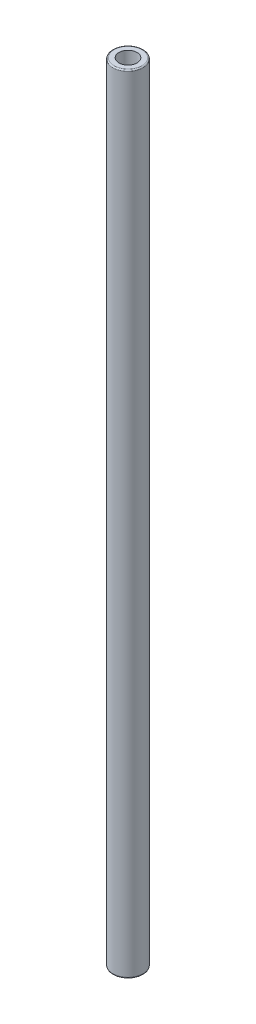
SolidWorks part; units mm, degrees
material "Thornel Mat VMA"
ref_plane "Front Plane" through (0, 0, 0) normal (0, 0, 1) x (1, 0, 0)
ref_plane "Top Plane" through (0, 0, 0) normal (0, 1, 0) x (1, 0, 0)
ref_plane "Right Plane" through (0, 0, 0) normal (1, 0, 0) x (0, 0, -1)
ref_plane "Front Plane-SSP" through (0, 0, 0) normal (0, 0, 1) x (1, 0, 0)
ref_plane "Top Plane-SSP" through (0, 0, 0) normal (0, 1, 0) x (1, 0, 0)
ref_plane "Right Plane-SSP" through (0, 0, 0) normal (1, 0, 0) x (0, 0, -1)
sketch "BagSide-SSP" plane through (0, 0, 0) normal (0, 0, 1) x (1, 0, 0)
  line L0 (0, 430) -> (0, 0)
  line L1 (0, 0) -> (179.1899, -17.0582)
  line L2 (179.1899, -17.0582) -> (130.767, 380)
  line L3 (130.767, 380) -> (0, 430)
  line L4 (130.767, 380) -> (0, 380)
  dimension "D1" = 430
  dimension "D2" = 140
  dimension "D3" = 400
  dimension "D4" = 180
  dimension "D5" = 50
  dimension "D6" = 17.0582
  dimension "D7" = 130.767
sketch "RodAndHolder-SSP" plane through (0, 0, 0) normal (0, 1, 0) x (1, 0, 0)
  circle A0 centre (0, 0) radius 1.5
  circle A1 centre (0, 0) radius 2.5
  circle A2 centre (0, 0) radius 2.75
  circle A3 centre (0, 0) radius 5
  point P9 (-5, 0)
  point P10 (-2.75, 0)
  point P11 (-2.5, 0)
  point P12 (-1.5, 0)
  point P13 (1.5, 0)
  point P14 (2.5, 0)
  point P15 (2.75, 0)
  point P16 (5, 0)
  dimension "D1" = 10
  dimension "D2" = 3
  dimension "D3" = 5
  dimension "RodHoleDiameter" = 5.5
sketch "RodAndHolderVertical-SSP" plane through (0, 0, 0) normal (0, 0, 1) x (1, 0, 0)
  line L2 (-5, 0) -> (-5, 15)
  line L3 (-2.5, 5) -> (-2.5, 20)
  line L5 (-5, 15) -> (-2.75, 15)
  line L7 (5, 0) -> (5, 15)
  line L12 (5, 15) -> (2.75, 15)
  line L13 (2.75, 15) -> (2.75, 5)
  line L14 (-2.75, 5) -> (-2.75, 15)
  line L15 (2.75, 5) -> (-2.75, 5)
  line L16 (2.5, 5) -> (2.5, 20)
  line L17 (-5, 0) -> (5, 0)
  dimension "D1" = 15
  dimension "D2" = 10
  dimension "RodHoleDepth" = 10
  dimension "D3" = 5.5
  dimension "D4" = 15
  dimension "D5" = 5
sketch "BagRear-SSP" plane through (0, 0, 0) normal (1, 0, 0) x (0, 0, -1)
  line L1 (0, 430) -> (0, 0)
  line L2 (0, 430) -> (270, 430)
  line L3 (270, 430) -> (270, 0)
  line L4 (270, 0) -> (0, 0)
  dimension "Width" = 270
inserted part "SSP"
sketch "SideRodLengths" plane through (0, 0, 0) normal (0, 0, 1) x (1, 0, 0)
  line L0 (0, 425) -> (0, 5)
  line L1 (0, 430) -> (0, 0) construction
  line L2 (4.6702, 428.2143) -> (126.0967, 381.7857)
  line L3 (130.767, 380) -> (0, 430) construction
  line L4 (131.3723, 375.0368) -> (178.5846, -12.095)
  line L5 (179.1899, -17.0582) -> (130.767, 380) construction
  line L6 (174.2124, -16.5844) -> (4.9775, -0.4738)
  line L7 (0, 0) -> (179.1899, -17.0582) construction
  line L8 (0, 430) -> (0, 425) construction
  line L9 (4.6702, 428.2143) -> (0, 430) construction
  line L10 (126.0967, 381.7857) -> (130.767, 380) construction
  line L11 (130.767, 380) -> (131.3723, 375.0368) construction
  line L12 (178.5846, -12.095) -> (179.1899, -17.0582) construction
  line L13 (179.1899, -17.0582) -> (174.2124, -16.5844) construction
  line L14 (4.9775, -0.4738) -> (0, 0) construction
  line L15 (0, 0) -> (0, 5) construction
  line L17 (0, 5) -> (0, 0) construction
  line L18 (2.75, 5) -> (-2.75, 5) construction
sketch "ConnectingRodLength" plane through (0, 0, 0) normal (1, 0, 0) x (0, 0, -1)
  line L0 (0, 0) -> (0, 5) construction
  line L1 (270, 0) -> (265, 0) construction
  line L2 (270, 0) -> (0, 0) construction
  line L3 (265, 0) -> (5, 0)
  line L4 (5, 0) -> (0, 0) construction
  line L7 (0, 430) -> (0, 0) construction
  dimension "Length" = 260
  dimension "D2" = 5
sketch "Sketch5" plane through (0, 0, 0) normal (0, 1, 0) x (1, 0, 0)
  circle A0 centre (0, 0) radius 1.5 construction
  circle A1 centre (0, 0) radius 2.5 construction
  circle A2 centre (0, 0) radius 1.5
  circle A3 centre (0, 0) radius 2.5
extrude "MainBody" add sketch "Sketch5" along normal mid plane 130
fillet "0.2mm" radius 0.2 2 edges at (0, -65, 2.5) (0, 65, 2.5)
